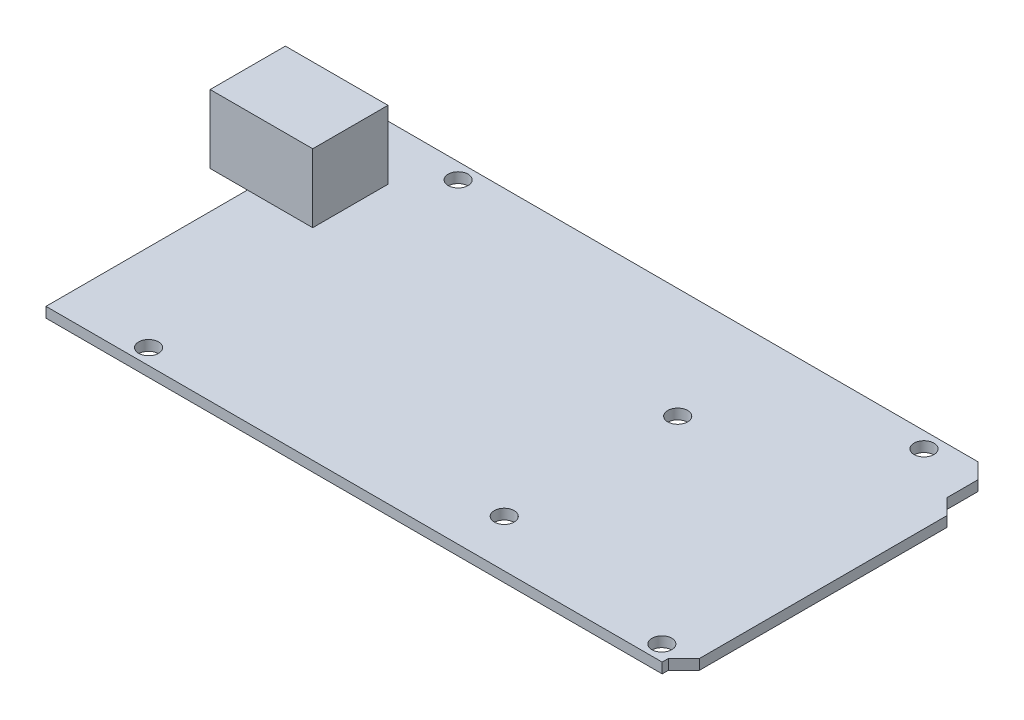
SolidWorks part; units mm, degrees
ref_plane "Front Plane" through (0, 0, 0) normal (0, 0, 1) x (1, 0, 0)
ref_plane "Top Plane" through (0, 0, 0) normal (0, 1, 0) x (1, 0, 0)
ref_plane "Right Plane" through (0, 0, 0) normal (1, 0, 0) x (0, 0, -1)
sketch "Sketch1" plane through (0, 0, 0) normal (0, 1, 0) x (1, 0, 0)
  line L0 (99.1, 0) -> (99.1, 1)
  line L1 (0, 0) -> (99.1, 0)
  line L2 (0, 0) -> (0, 53.3)
  line L3 (0, 53.3) -> (96.6, 53.3)
  line L5 (99.1, 1) -> (101.6, 3.5)
  line L6 (101.6, 3.5) -> (101.6, 43.3)
  line L7 (101.6, 43.3) -> (99.1, 45.8)
  line L8 (99.1, 45.8) -> (99.1, 50.8)
  line L9 (99.1, 50.8) -> (96.6, 53.3)
  circle A0 centre (15.524, 50.76) radius 1.6
  circle A1 centre (14, 2.5) radius 1.6
  circle A2 centre (96.55, 2.5) radius 1.6
  circle A3 centre (90.454, 50.76) radius 1.6
  circle A4 centre (66.1, 35.5) radius 1.6
  circle A5 centre (66.1, 7.6) radius 1.6
  dimension "D3" = 3.2
  dimension "D4" = 14
  dimension "D7" = 27.9
  dimension "D10" = 52.1
  dimension "D11" = 76.454
  dimension "D8" = 5.1
  dimension "D1" = 53.3
  dimension "D2" = 101.6
  dimension "D5" = 1.524
  dimension "D6" = 2.5
  dimension "D9" = 48.26
  dimension "D12" = 1
  dimension "D13" = 2.5
  dimension "D14" = 10
  dimension "D15" = 45
  dimension "D16" = 82.55
extrude "Boss-Extrude1" add sketch "Sketch1" along normal blind 1.65
sketch "Sketch2" plane through (0, 1.65, 0) normal (0, 1, 0) x (1, 0, 0)
  line L0 (96.6, 53.3) -> (0, 53.3) construction
  line L1 (-6, 44.5) -> (10.5, 44.5)
  line L2 (-6, 44.5) -> (-6, 32.4)
  line L3 (-6, 32.4) -> (10.5, 32.4)
  line L4 (10.5, 44.5) -> (10.5, 32.4)
  line L5 (0, 53.3) -> (0, 0) construction
  dimension "D1" = 12.1
  dimension "D2" = 16.5
  dimension "D3" = 8.8
  dimension "D4" = 6
extrude "Boss-Extrude2" add sketch "Sketch2" along normal blind 11
